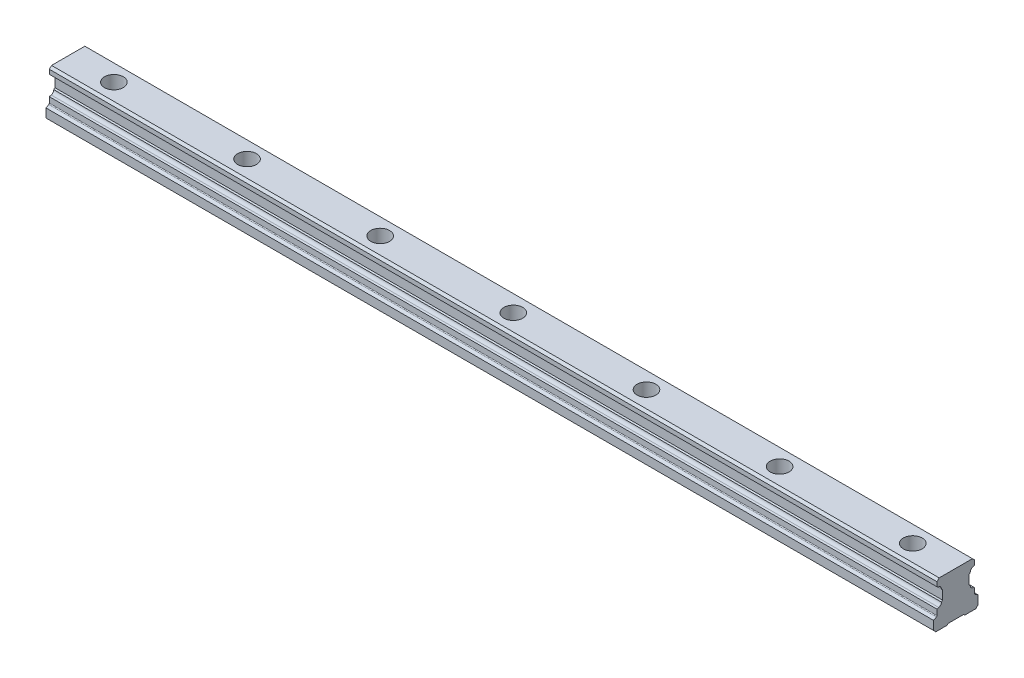
SolidWorks part; units mm, degrees
ref_plane "Front Plane" through (0, 0, 0) normal (0, 0, 1) x (1, 0, 0)
ref_plane "Top Plane" through (0, 0, 0) normal (0, 1, 0) x (1, 0, 0)
ref_plane "Right Plane" through (0, 0, 0) normal (1, 0, 0) x (0, 0, -1)
ref_plane "Plane1" through (58.5, 0, 0) normal (1, 0, 0) x (0, 0, -1)
sketch "Sketch7" plane through (58.5, 0, 0) normal (1, 0, 0) x (0, 0, -1)
  line L30 (-7.709, 8.8831) -> (-8.5, 8.6011)
  line L32 (-8.75, 5.6717) -> (-10, 4.95)
  line L35 (-10, 4.95) -> (-10, 1)
  line L37 (-10, 1) -> (-9, 0)
  line L39 (-4, 0) -> (-3.5, 0.5)
  line L42 (-3.5, 0.5) -> (3.5, 0.5)
  line L48 (3.5, 0.5) -> (4, 0)
  line L52 (4, 0) -> (9, 0)
  line L57 (-8.5, 8.6011) -> (-8.5, 6.1047)
  line L61 (-9, 0) -> (-4, 0)
  line L69 (8.5, 6.1047) -> (8.5, 8.4669)
  line L71 (6.5033, 10.3667) -> (6, 10.87)
  line L72 (6, 10.87) -> (6, 14.93)
  line L73 (6, 14.93) -> (6.5033, 15.4333)
  line L75 (8.5, 17.1989) -> (8.5, 19.3)
  line L77 (7.5, 20.3) -> (-7.5, 20.3)
  line L79 (-8.5, 19.3) -> (-8.5, 17.3331)
  line L81 (-6.5033, 15.4333) -> (-6, 14.93)
  line L82 (-6, 14.93) -> (-6, 10.87)
  line L83 (-6, 10.87) -> (-6.5033, 10.3667)
  line L85 (9, 0) -> (10, 1)
  line L87 (10, 1) -> (10, 4.95)
  line L89 (10, 4.95) -> (8.75, 5.6717)
  line L91 (8.5, 8.4669) -> (8.0847, 8.8822)
  line L93 (7.709, 16.9169) -> (8.5, 17.1989)
  line L95 (8.5, 19.3) -> (7.5, 20.3)
  line L97 (-7.5, 20.3) -> (-8.5, 19.3)
  line L99 (-8.5, 17.3331) -> (-8.0847, 16.9178)
  arc A8 (-8.75, 5.6717) -> (-8.5, 6.1047) centre (-9, 6.1047) ccw
  arc A12 (-7.709, 8.8831) -> (-6.5033, 10.3667) centre (-7.9, 10.27) ccw
  arc A15 (6.5033, 10.3667) -> (8.0847, 8.8822) centre (7.9, 10.27) ccw
  arc A16 (7.709, 16.9169) -> (6.5033, 15.4333) centre (7.9, 15.53) ccw
  arc A17 (-6.5033, 15.4333) -> (-8.0847, 16.9178) centre (-7.9, 15.53) ccw
  arc A19 (8.5, 6.1047) -> (8.75, 5.6717) centre (9, 6.1047) ccw
sketch "Sketch1" [suppressed] plane through (58.5, 0, 0) normal (1, 0, 0) x (0, 0, -1)
  line L0 (-8.5, 0) -> (8.5, 0)
  line L1 (8.5, 0) -> (8.5, 9.0051)
  line L2 (6.5033, 10.3667) -> (6, 10.87)
  line L3 (6, 10.87) -> (6, 14.93)
  line L4 (6, 14.93) -> (6.5033, 15.4333)
  line L5 (8.5, 16.7949) -> (8.5, 20.3)
  line L6 (8.5, 20.3) -> (-8.5, 20.3)
  line L7 (-8.5, 20.3) -> (-8.5, 16.7949)
  line L8 (-6.5033, 15.4333) -> (-6, 14.93)
  line L9 (-6, 14.93) -> (-6, 10.87)
  line L10 (-6, 10.87) -> (-6.5033, 10.3667)
  line L11 (-8.5, 9.0051) -> (-8.5, 0)
  arc A0 (8.5, 9.0051) -> (6.5033, 10.3667) centre (7.9, 10.27) cw
  arc A1 (6.5033, 15.4333) -> (8.5, 16.7949) centre (7.9, 15.53) cw
  arc A2 (-8.5, 16.7949) -> (-6.5033, 15.4333) centre (-7.9, 15.53) cw
  arc A3 (-6.5033, 10.3667) -> (-8.5, 9.0051) centre (-7.9, 10.27) cw
extrude "Boss-Extrude5" add sketch "Sketch7" along normal blind 400
sketch "Sketch8" plane through (0, 20.3, 0) normal (0, 1, 0) x (1, 0, 0)
  line L0 (58.5, 7.5) -> (58.5, -7.5) construction
  circle A0 centre (79.1, 0) radius 4.25
  dimension "D1" = 8.5
  dimension "D2" = 20.6
extrude "Cut-Extrude1" cut sketch "Sketch8" against normal blind 9
sketch "Sketch9" plane through (0, 11.3, 0) normal (0, 1, 0) x (1, 0, 0)
  circle A0 centre (79.1, 0) radius 3
  dimension "D1" = 6
extrude "Cut-Extrude2" cut sketch "Sketch9" against normal through all
pattern_linear "LPattern1" count 20 spacing 60 along (1, 0, 0) of "Cut-Extrude1", "Cut-Extrude2"
